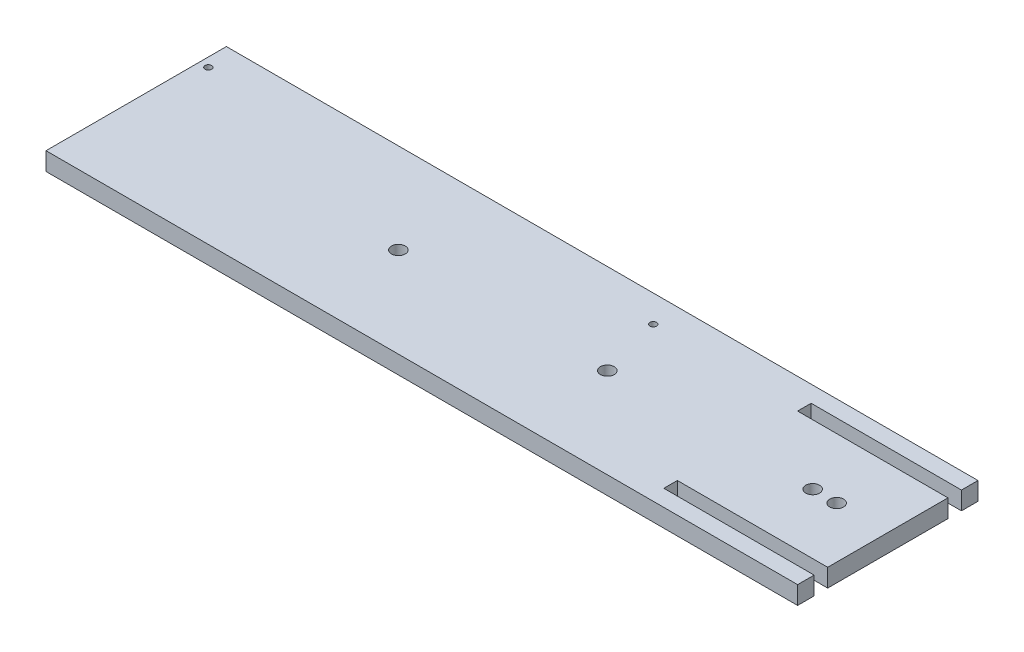
SolidWorks part; units mm, degrees
ref_plane "Front Plane" through (0, 0, 0) normal (0, 0, 1) x (1, 0, 0)
ref_plane "Top Plane" through (0, 0, 0) normal (0, 1, 0) x (1, 0, 0)
ref_plane "Right Plane" through (0, 0, 0) normal (1, 0, 0) x (0, 0, -1)
sketch "Sketch1" plane through (0, 0, 0) normal (0, 1, 0) x (1, 0, 0)
  line L1 (-125, 30) -> (125, 30)
  line L2 (-125, 30) -> (-125, -30)
  line L3 (-125, -30) -> (125, -30)
  line L4 (125, 30) -> (125, -30)
  line L5 (-125, 30) -> (125, -30) construction
  line L6 (-125, -30) -> (125, 30) construction
  circle A0 centre (108, 0) radius 2.3
  circle A1 centre (100, 0) radius 2.3
  circle A2 centre (31.7, 0) radius 2.3
  circle A3 centre (-37.8, 0) radius 2.3
  point P0 (0, 0)
  dimension "D3" = 17
  dimension "D5" = 4.6
  dimension "D6" = 4.6
  dimension "D8" = 4.6
  dimension "D9" = 137.8
  dimension "D10" = 4.6
  dimension "D1" = 60
  dimension "D2" = 250
  dimension "D4" = 8
  dimension "D7" = 68.3
extrude "Boss-Extrude1" add sketch "Sketch1" along normal blind 6
sketch "Sketch2" plane through (0, 6, 0) normal (0, 1, 0) x (1, 0, 0)
  line L0 (125, -30) -> (125, 30) construction
  line L1 (125, -20) -> (75, -20)
  line L2 (125, -20) -> (125, -24.5)
  line L3 (125, -24.5) -> (75, -24.5)
  line L4 (75, -20) -> (75, -24.5)
  line L6 (125, 20) -> (75, 20)
  line L7 (125, 20) -> (125, 24.5)
  line L8 (125, 24.5) -> (75, 24.5)
  line L9 (75, 20) -> (75, 24.5)
  circle A0 centre (108, 0) radius 2.3 construction
  dimension "D1" = 20
  dimension "D2" = 20
  dimension "D3" = 4.5
  dimension "D4" = 4.5
  dimension "D5" = 50
  dimension "D6" = 50
extrude "Cut-Extrude1" cut sketch "Sketch2" against normal blind 6
sketch "Sketch3" plane through (0, 0, 0) normal (0, -1, 0) x (1, 0, 0)
  line L0 (-125, -30) -> (-125, 30) construction
  circle A0 centre (-122, -21) radius 1.1
  circle A1 centre (26, -21) radius 1.1
  circle A2 centre (-37.8, 0) radius 2.3 construction
  dimension "D1" = 3
  dimension "D2" = 2.2
  dimension "D3" = 21
  dimension "D5" = 2.2
  dimension "D6" = 148
  dimension "D4" = 21
extrude "Cut-Extrude2" cut sketch "Sketch3" against normal blind 10
